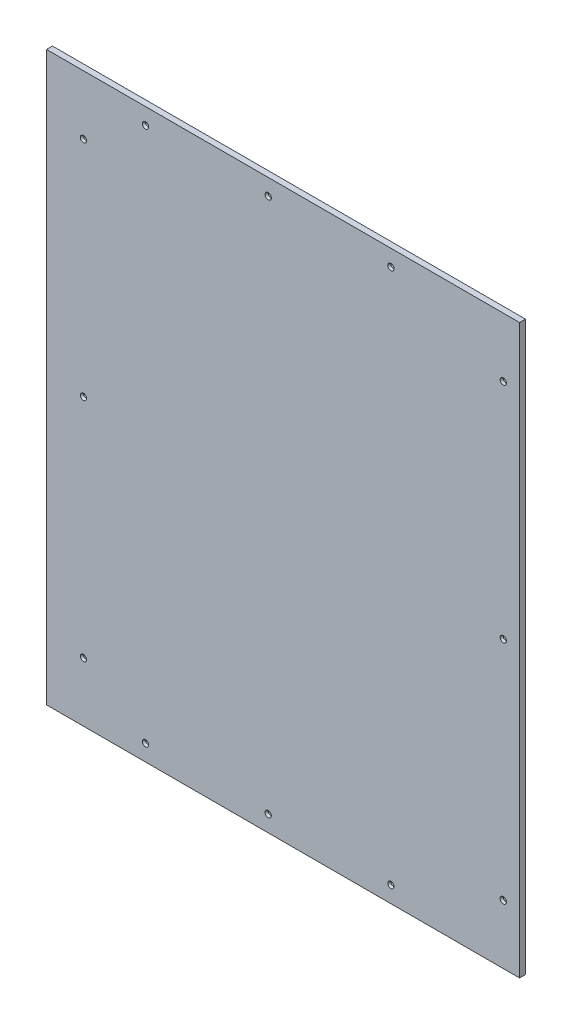
SolidWorks part; units mm, degrees
material "PE High Density"
ref_plane "Front Plane" through (0, 0, 0) normal (0, 0, 1) x (1, 0, 0)
ref_plane "Top Plane" through (0, 0, 0) normal (0, 1, 0) x (1, 0, 0)
ref_plane "Right Plane" through (0, 0, 0) normal (1, 0, 0) x (0, 0, -1)
sketch "Sketch1" plane through (0, 0, 0) normal (0, 0, 1) x (1, 0, 0)
  line L1 (-106.2888, 1219.2) -> (-1122.2888, 1219.2)
  line L2 (-106.2888, 1219.2) -> (-106.2888, 0)
  line L3 (-106.2888, 0) -> (-1122.2888, 0)
  line L4 (-1122.2888, 1219.2) -> (-1122.2888, 0)
  line L5 (-106.2888, 1219.2) -> (-106.2888, 0) construction
  dimension "D1" = 1016
  dimension "D2" = 1219.2
extrude "Boss-Extrude1" add sketch "Sketch1" along normal blind 12.7
sketch "Sketch2" plane through (0, 0, 0) normal (0, 0, -1) x (-1, 0, 0)
  line L0 (106.2888, 1219.2) -> (1122.2888, 1219.2) construction
  line L1 (106.2888, 0) -> (106.2888, 1219.2) construction
  line L2 (106.2888, 1219.2) -> (1122.2888, 1219.2) construction
  line L3 (1122.2888, 609.6) -> (106.2888, 609.6) construction
  line L4 (106.2888, 0) -> (106.2888, 1219.2) construction
  line L5 (1122.2888, 1219.2) -> (1122.2888, 0) construction
  circle A18 centre (382.6408, 1184.275) radius 3.302
  circle A19 centre (646.1658, 1184.275) radius 3.302
  circle A20 centre (909.6908, 1184.275) radius 3.302
  circle A41 centre (1042.914, 1092.073) radius 3.175 construction
  circle A43 centre (1042.914, 127) radius 3.175 construction
  circle A47 centre (141.2138, 127.127) radius 3.175 construction
  circle A49 centre (141.2138, 1092.073) radius 3.175 construction
  circle A50 centre (1042.914, 1092.073) radius 3.175
  circle A51 centre (1042.914, 612.775) radius 3.175
  circle A52 centre (1042.914, 127) radius 3.175
  circle A56 centre (141.2138, 127.127) radius 3.175
  circle A57 centre (141.2138, 612.775) radius 3.302
  circle A58 centre (141.2138, 1092.073) radius 3.175
  circle A59 centre (909.6908, 34.925) radius 3.302
  circle A60 centre (646.1658, 34.925) radius 3.302
  circle A61 centre (382.6408, 34.925) radius 3.302
  dimension "D2" = 6.604
  dimension "D4" = 263.525
  dimension "D6" = 606.425
  dimension "D7" = 34.925
  dimension "D8" = 6.604
  dimension "D1" = 276.352
  dimension "D3" = 263.525
  dimension "D5" = 34.925
  dimension "D9" = 479.298
extrude "Cut-Extrude1" cut sketch "Sketch2" against normal blind 12.7
hole_wizard "CSK for 1/4 Flat Head Socket Cap Screw1" positions "3DSketch1" profile "Sketch3" countersink size "1/4" standard "ANSI Inch" end condition through all
sketch3d "3DSketch1"
  line L0 (-909.6908, 1184.275, 12.7) -> (-909.6908, 1184.275, 0) construction
  line L1 (-646.1658, 1184.275, 12.7) -> (-646.1658, 1184.275, 0) construction
  line L2 (-382.6408, 1184.275, 12.7) -> (-382.6408, 1184.275, 0) construction
  line L3 (-141.2138, 1092.073, 12.7) -> (-141.2138, 1092.073, 0) construction
  line L4 (-141.2138, 612.775, 12.7) -> (-141.2138, 612.775, 0) construction
  line L5 (-141.2138, 127.127, 12.7) -> (-141.2138, 127.127, 0) construction
  line L6 (-382.6408, 34.925, 12.7) -> (-382.6408, 34.925, 0) construction
  line L7 (-646.1658, 34.925, 12.7) -> (-646.1658, 34.925, 0) construction
  line L8 (-909.6908, 34.925, 12.7) -> (-909.6908, 34.925, 0) construction
  line L9 (-1042.914, 127, 12.7) -> (-1042.914, 127, 0) construction
  line L10 (-1042.914, 612.775, 12.7) -> (-1042.914, 612.775, 0) construction
  line L11 (-1042.914, 1092.073, 12.7) -> (-1042.914, 1092.073, 0) construction
  point P0 (-909.6908, 1184.275, 12.7)
  point P4 (-646.1658, 1184.275, 12.7)
  point P8 (-382.6408, 1184.275, 12.7)
  point P12 (-141.2138, 1092.073, 12.7)
  point P16 (-141.2138, 612.775, 12.7)
  point P20 (-141.2138, 127.127, 12.7)
  point P24 (-382.6408, 34.925, 12.7)
  point P28 (-646.1658, 34.925, 12.7)
  point P32 (-909.6908, 34.925, 12.7)
  point P36 (-1042.914, 127, 12.7)
  point P40 (-1042.914, 612.775, 12.7)
  point P44 (-1042.914, 1092.073, 12.7)
sketch "Sketch3" plane through (-909.6908, 1184.275, 12.7) normal (1, 0, 0) x (0, -1, 0)
  line L0 (0, 0) -> (0, 12.7)
  line L1 (0, 12.7) -> (3.3782, 12.7)
  line L2 (3.3782, 12.7) -> (3.3782, 3.8716)
  line L3 (3.3782, 3.8716) -> (6.7437, 0)
  line L5 (6.7437, 0) -> (0, 0)
  line L6 (-3.3782, 3.8716) -> (-6.7437, 0) construction
  line L11 (0, -6.35) -> (0, 107.95) construction
  dimension "Thru Hole Dia." = 6.7564
  dimension "Thru Hole Depth" = 12.7
  dimension "Near C'Sink Dia." = 13.4874
  dimension "Near C'Sink Angle" = 82
